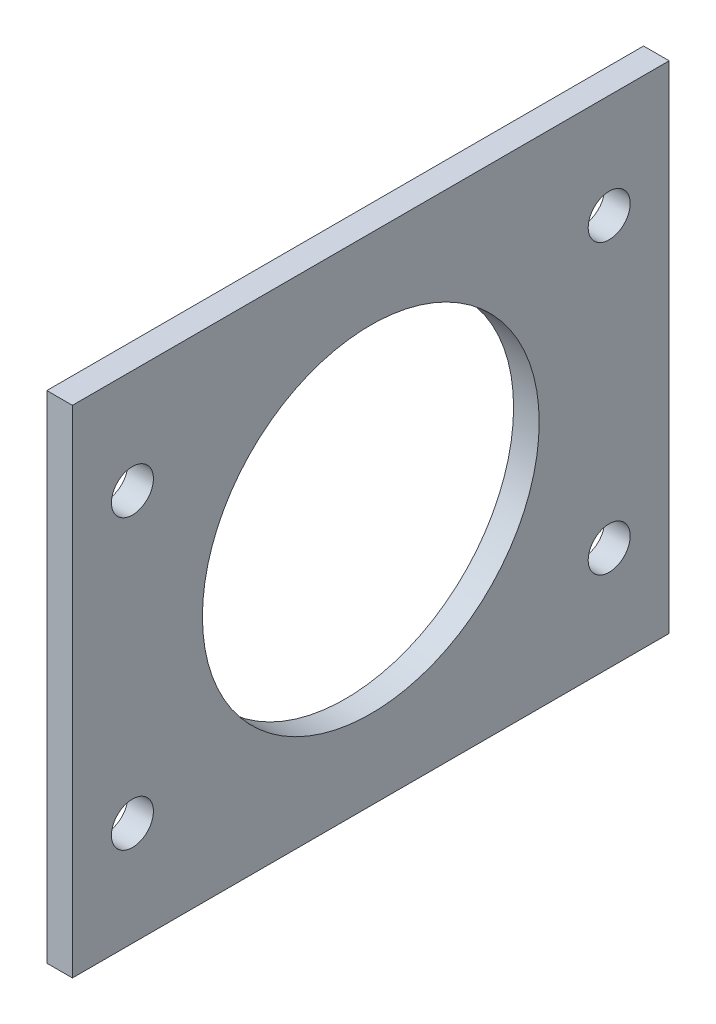
SolidWorks part; units mm, degrees
material "AISI 304"
ref_plane "Front Plane" through (0, 0, 0) normal (0, 0, 1) x (1, 0, 0)
ref_plane "Top Plane" through (0, 0, 0) normal (0, 1, 0) x (1, 0, 0)
ref_plane "Right Plane" through (0, 0, 0) normal (1, 0, 0) x (0, 0, -1)
sketch "Sketch1" plane through (0, 0, 0) normal (1, 0, 0) x (0, 0, -1)
  line L1 (0, 0) -> (74.6, 0)
  line L2 (0, 0) -> (0, 62)
  line L3 (0, 62) -> (74.6, 62)
  line L4 (74.6, 0) -> (74.6, 62)
  dimension "D1" = 74.6
  dimension "D2" = 62
extrude "Boss-Extrude1" add sketch "Sketch1" along normal blind 3.2
sketch "Sketch2" plane through (3.2, 0, 0) normal (1, 0, 0) x (0, 0, -1)
  line L0 (37.3, 62) -> (37.3, 0) construction
  line L1 (74.6, 62) -> (0, 62) construction
  line L2 (0, 0) -> (74.6, 0) construction
  circle A0 centre (37.3, 31) radius 21.05
  point P13 (37.3, 0)
  dimension "D1" = 21.05
extrude "Cut-Extrude1" cut sketch "Sketch2" against normal up to next
sketch "Sketch3" plane through (0, 0, 0) normal (-1, 0, 0) x (0, 0, 1)
  circle A0 centre (-67.1, 13) radius 2.625
  circle A1 centre (-67.1, 49) radius 2.625
  circle A2 centre (-7.5, 13) radius 2.625
  circle A3 centre (-7.5, 49) radius 2.625
extrude "Cut-Extrude2" cut sketch "Sketch3" against normal up to next
